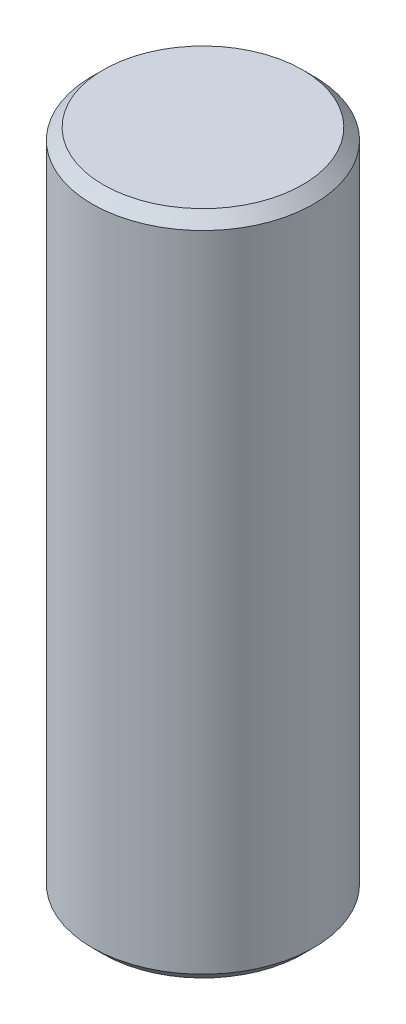
SolidWorks part; units mm, degrees
ref_plane "Front Plane" through (0, 0, 0) normal (0, 0, 1) x (1, 0, 0)
ref_plane "Top Plane" through (0, 0, 0) normal (0, 1, 0) x (1, 0, 0)
ref_plane "Right Plane" through (0, 0, 0) normal (1, 0, 0) x (0, 0, -1)
sketch "Sketch1" plane through (0, 0, 0) normal (0, 1, 0) x (1, 0, 0)
  circle A0 centre (0, 0) radius 2.49
  dimension "D1" = 4.98
extrude "Boss-Extrude1" add sketch "Sketch1" along normal blind 14.98
chamfer "Chamfer1" distance 0.25 angle 45 2 edges at (0, 0, 2.49) (0, 14.98, 2.49)
